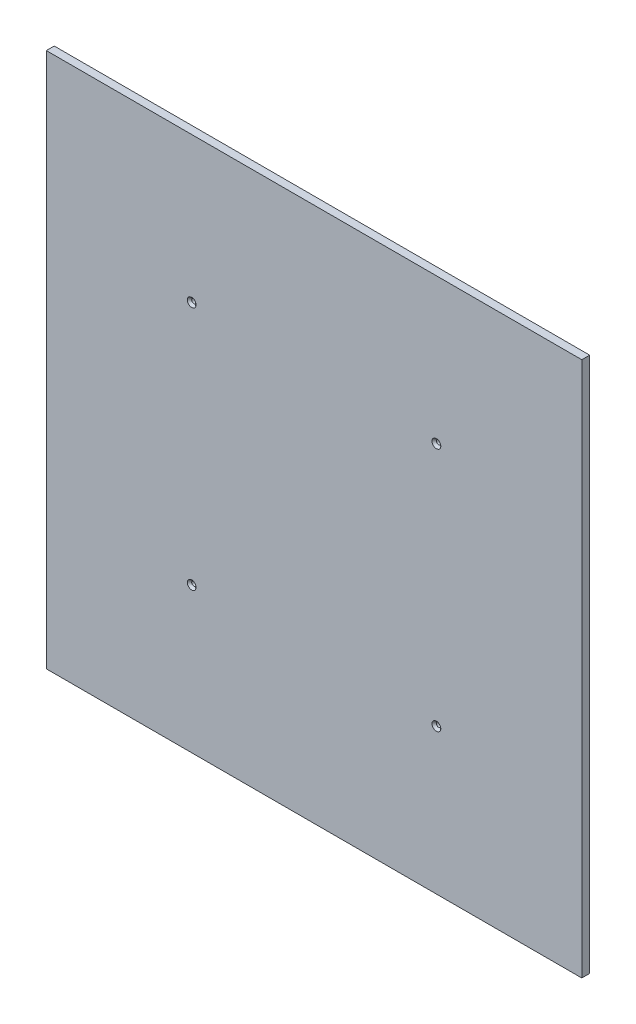
SolidWorks part; units mm, degrees
material "Pine"
ref_plane "Front Plane" through (0, 0, 0) normal (0, 0, 1) x (1, 0, 0)
ref_plane "Top Plane" through (0, 0, 0) normal (0, 1, 0) x (1, 0, 0)
ref_plane "Right Plane" through (0, 0, 0) normal (1, 0, 0) x (0, 0, -1)
sketch "Sketch1" plane through (0, 0, 0) normal (0, 0, 1) x (1, 0, 0)
  line L1 (610, -610) -> (-610, -610)
  line L2 (610, -610) -> (610, 610)
  line L3 (610, 610) -> (-610, 610)
  line L4 (-610, -610) -> (-610, 610)
  line L5 (610, -610) -> (-610, 610) construction
  line L6 (610, 610) -> (-610, -610) construction
  point P0 (0, 0)
  dimension "D1" = 1220
extrude "Boss-Extrude1" add sketch "Sketch1" against normal blind 18 from offset 8
sketch "Sketch2" plane through (0, 0, -10) normal (0, 0, -1) x (-1, 0, 0)
  circle A0 centre (-278.7635, 278.7635) radius 5
  circle A1 centre (-278.7635, -278.7635) radius 5
  circle A2 centre (278.7635, -278.7635) radius 5
  circle A3 centre (278.7635, 278.7635) radius 5
  dimension "D1" = 10
extrude "Cut-Extrude1" cut sketch "Sketch2" against normal through all
chamfer "Chamfer1" distance 5 angle 45 4 edges at (273.7635, 278.7635, 8) (-283.7635, 278.7635, 8) (-283.7635, -278.7635, 8) (273.7635, -278.7635, 8)
